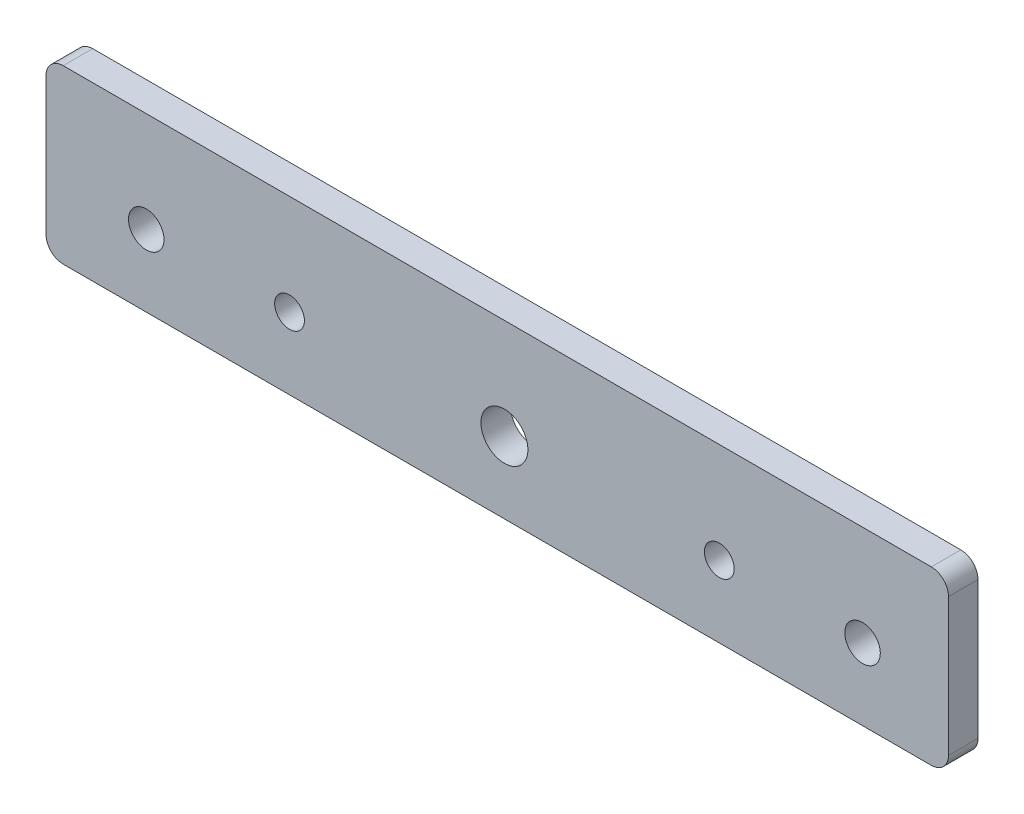
SolidWorks part; units mm, degrees
ref_plane "Front Plane" through (0, 0, 0) normal (0, 0, 1) x (1, 0, 0)
ref_plane "Top Plane" through (0, 0, 0) normal (0, 1, 0) x (1, 0, 0)
ref_plane "Right Plane" through (0, 0, 0) normal (1, 0, 0) x (0, 0, -1)
sketch "Sketch1" plane through (0, 0, 0) normal (0, 0, 1) x (1, 0, 0)
  line L0 (-77, 17.5) -> (74.5, 17.5)
  line L1 (-77, -12.5) -> (74.5, -12.5)
  line L2 (-80, -9.5) -> (-80, 14.5)
  line L3 (77.5, 14.5) -> (77.5, -9.5)
  circle A0 centre (-37.5, 0) radius 2.6
  circle A1 centre (37.5, 0) radius 2.6
  circle A2 centre (-62.5, 0) radius 3.1
  circle A3 centre (62.5, 0) radius 3.1
  circle A4 centre (0, 0) radius 4.1
  arc A5 (77.5, 14.5) -> (74.5, 17.5) centre (74.5, 14.5) ccw
  arc A6 (74.5, -12.5) -> (77.5, -9.5) centre (74.5, -9.5) ccw
  arc A7 (-77, -12.5) -> (-80, -9.5) centre (-77, -9.5) cw
  arc A8 (-77, 17.5) -> (-80, 14.5) centre (-77, 14.5) ccw
  arc A9 (-80, 14.5) -> (-77, 17.5) centre (-77, 14.5) cw
  dimension "D1" = 75
  dimension "D4" = 5.2
  dimension "D5" = 25
  dimension "D7" = 3
  dimension "D8" = 3
  dimension "D12" = 8.2
  dimension "D13" = 6.2
  dimension "D2" = 17.5
  dimension "D3" = 12.5
  dimension "D6" = 25
  dimension "D9" = 80
  dimension "D10" = 37.5
  dimension "D11" = 40
extrude "Boss-Extrude1" add sketch "Sketch1" along normal blind 5.15 contours L0 A8 L2 A7 L1 A6 L3 A5 A0 A1 A2 A3 A4
